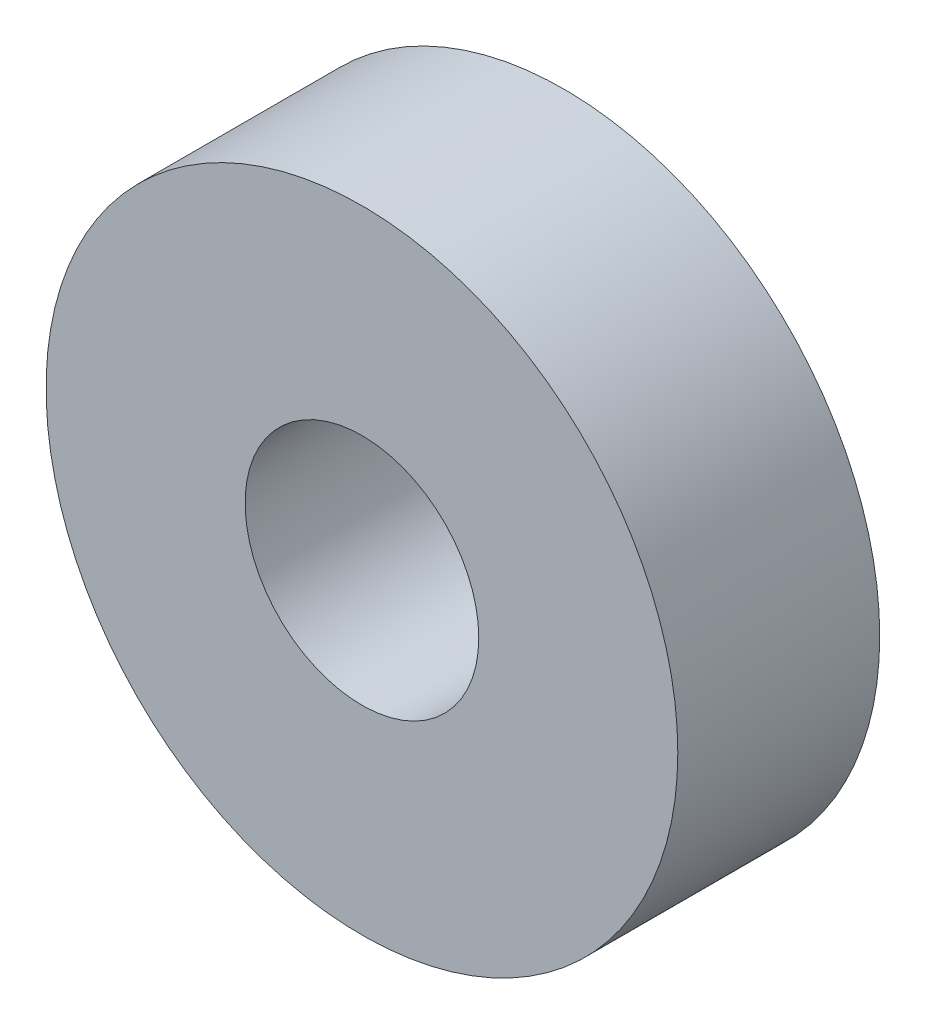
SolidWorks part; units mm, degrees
ref_plane "Front" through (0, 0, 0) normal (0, 0, 1) x (1, 0, 0)
ref_plane "Top" through (0, 0, 0) normal (0, 1, 0) x (1, 0, 0)
ref_plane "Right" through (0, 0, 0) normal (1, 0, 0) x (0, 0, -1)
sketch "Эскиз1" plane through (0, 0, 0) normal (0, 0, 1) x (1, 0, 0)
  circle A0 centre (0, 0) radius 4.05
  circle A1 centre (0, 0) radius 10.95
  dimension "D1" = 8.1
  dimension "D2" = 21.9
extrude "Бобышка-Вытянуть1" add sketch "Эскиз1" along normal blind 7
